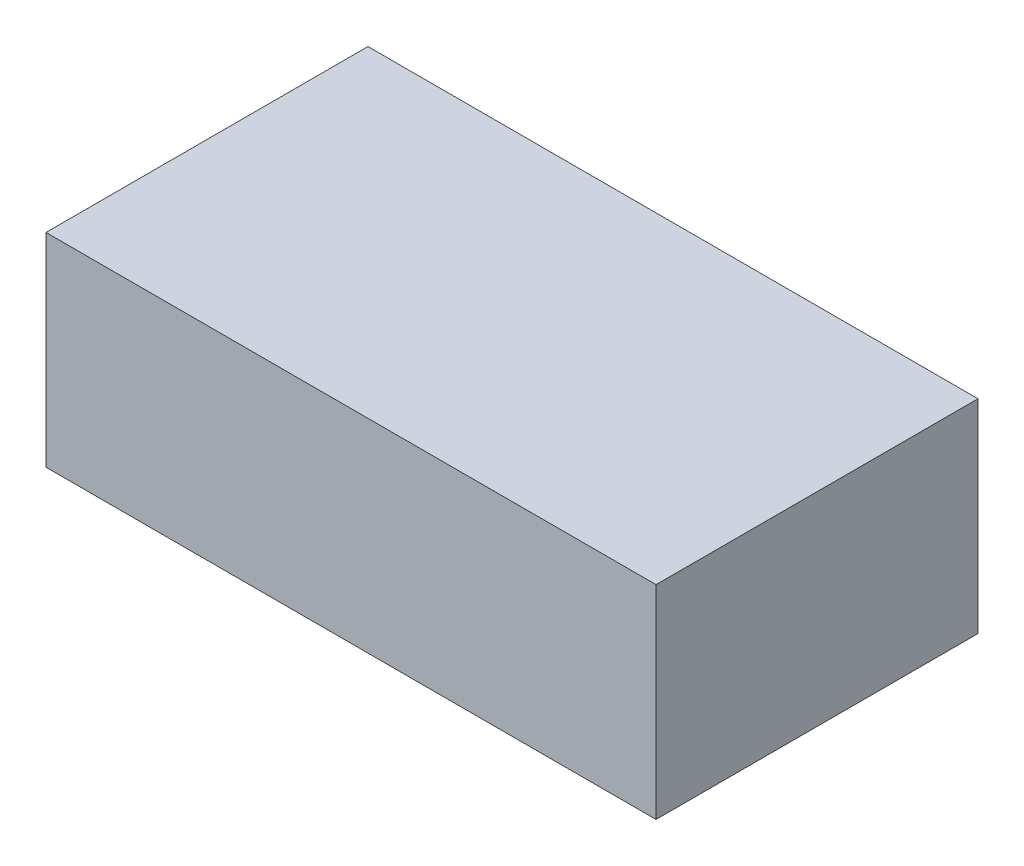
SolidWorks part; units mm, degrees
ref_plane "Front Plane" through (0, 0, 0) normal (0, 0, 1) x (1, 0, 0)
ref_plane "Top Plane" through (0, 0, 0) normal (0, 1, 0) x (1, 0, 0)
ref_plane "Right Plane" through (0, 0, 0) normal (1, 0, 0) x (0, 0, -1)
sketch "Sketch1" plane through (0, 0, 0) normal (0, 1, 0) x (1, 0, 0)
  line L1 (0, 0) -> (91.44, 0)
  line L2 (0, 0) -> (0, 48.26)
  line L3 (0, 48.26) -> (91.44, 48.26)
  line L4 (91.44, 0) -> (91.44, 48.26)
  dimension "D1" = 91.44
  dimension "D2" = 48.26
extrude "Boss-Extrude1" add sketch "Sketch1" along normal blind 30.48
